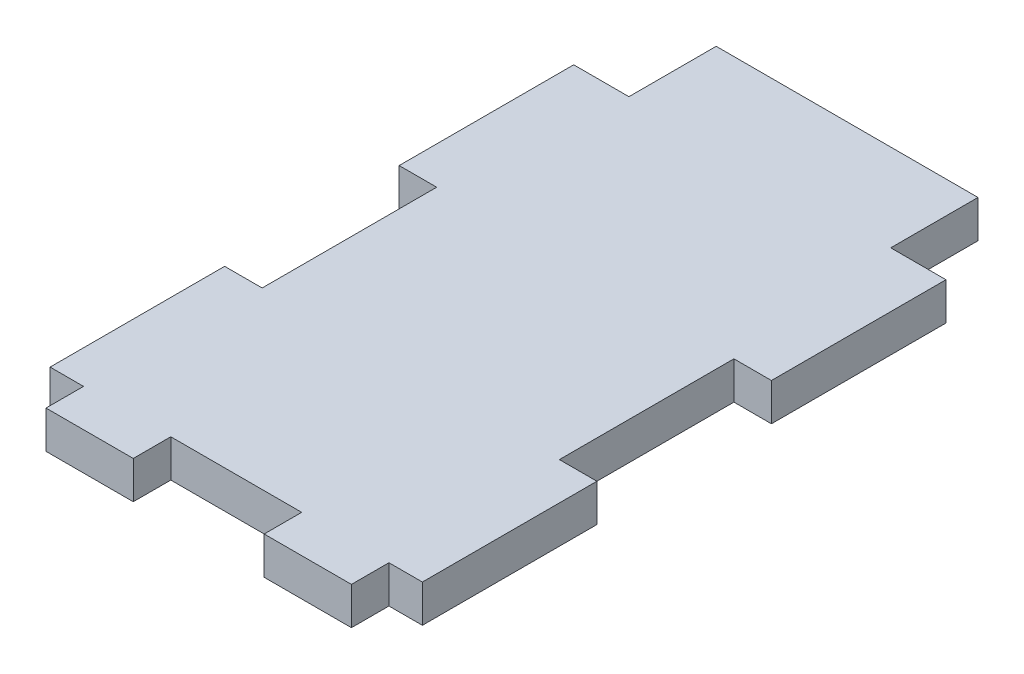
SolidWorks part; units mm, degrees
ref_plane "Front Plane" through (0, 0, 0) normal (0, 0, 1) x (1, 0, 0)
ref_plane "Top Plane" through (0, 0, 0) normal (0, 1, 0) x (1, 0, 0)
ref_plane "Right Plane" through (0, 0, 0) normal (1, 0, 0) x (0, 0, -1)
sketch "Sketch1" plane through (0, 0, 0) normal (0, 1, 0) x (1, 0, 0)
  line L1 (-27.0891, 38.1) -> (27.0891, 38.1)
  line L2 (-27.0891, 38.1) -> (-27.0891, -38.1)
  line L3 (-27.0891, -38.1) -> (27.0891, -38.1)
  line L4 (27.0891, 38.1) -> (27.0891, -38.1)
  line L5 (-27.0891, 38.1) -> (27.0891, -38.1) construction
  line L6 (-27.0891, -38.1) -> (27.0891, 38.1) construction
  point P0 (0, 0)
  dimension "D1" = 54.1782
  dimension "D2" = 76.2
extrude "Boss-Extrude1" add sketch "Sketch1" along normal blind 5.461
sketch "Sketch2" plane through (0, 5.461, 0) normal (0, 1, 0) x (1, 0, 0)
  line L0 (-27.0891, -38.1) -> (27.0891, -38.1) construction
  line L1 (-22.225, -38.1) -> (-9.525, -38.1)
  line L2 (-22.225, -38.1) -> (-22.225, -43.561)
  line L3 (-22.225, -43.561) -> (-9.525, -43.561)
  line L4 (-9.525, -38.1) -> (-9.525, -43.561)
  line L5 (-9.525, -38.1) -> (9.525, -38.1) construction
  line L6 (9.525, -38.1) -> (22.225, -38.1)
  line L7 (9.525, -38.1) -> (9.525, -43.561)
  line L8 (9.525, -43.561) -> (22.225, -43.561)
  line L9 (22.225, -38.1) -> (22.225, -43.561)
  line L20 (27.0891, 38.1) -> (-27.0891, 38.1) construction
  line L21 (-19.05, 38.1) -> (19.05, 38.1)
  line L22 (-19.05, 38.1) -> (-19.05, 50.8)
  line L23 (-19.05, 50.8) -> (19.05, 50.8)
  line L24 (19.05, 38.1) -> (19.05, 50.8)
  point P10 (0, -38.1)
  point P30 (0, 38.1)
  dimension "D1" = 5.461
  dimension "D2" = 12.7
  dimension "D3" = 19.05
  dimension "D4" = 12.7
  dimension "D5" = 38.1
extrude "Boss-Extrude2" add sketch "Sketch2" against normal up to surface (5.461 mm away) up to face at (0, 0, 0)
sketch "Sketch3" plane through (0, 5.461, 0) normal (0, 1, 0) x (1, 0, 0)
  line L0 (-27.0891, 38.1) -> (-27.0891, -38.1) construction
  line L1 (-27.0891, 12.7) -> (-21.6281, 12.7)
  line L2 (-27.0891, 12.7) -> (-27.0891, -12.7)
  line L3 (-27.0891, -12.7) -> (-21.6281, -12.7)
  line L4 (-21.6281, 12.7) -> (-21.6281, -12.7)
  line L5 (27.0891, -38.1) -> (27.0891, 38.1) construction
  line L6 (27.0891, 12.7) -> (21.6281, 12.7)
  line L7 (27.0891, 12.7) -> (27.0891, -12.7)
  line L8 (27.0891, -12.7) -> (21.6281, -12.7)
  line L9 (21.6281, 12.7) -> (21.6281, -12.7)
  point P12 (-27.0891, 0)
  dimension "D1" = 5.461
  dimension "D2" = 25.4
extrude "Cut-Extrude1" cut sketch "Sketch3" against normal through all
